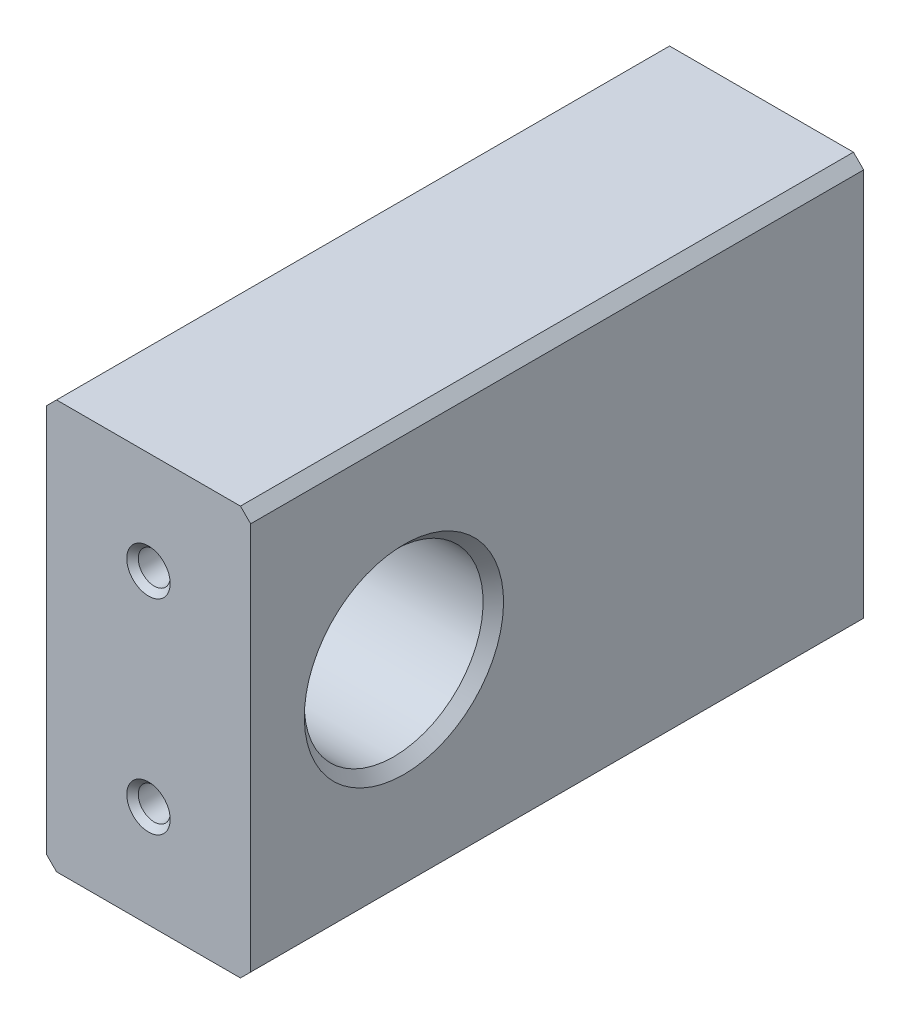
SolidWorks part; units mm, degrees
material "6061 Alloy"
ref_plane "Front" through (0, 0, 0) normal (0, 0, 1) x (1, 0, 0)
ref_plane "Top" through (0, 0, 0) normal (0, 1, 0) x (1, 0, 0)
ref_plane "Right" through (0, 0, 0) normal (1, 0, 0) x (0, 0, -1)
sketch "Sketch1" plane through (0, 0, 0) normal (0, 0, 1) x (1, 0, 0)
  line L0 (50.8, 0) -> (0, 0) construction
  line L1 (50.8, 50.8) -> (0, 50.8)
  line L2 (50.8, 50.8) -> (50.8, -50.8)
  line L3 (50.8, -50.8) -> (0, -50.8)
  line L4 (0, 50.8) -> (0, -50.8)
  dimension "D1" = 101.6
  dimension "D2" = 50.8
extrude "Extrude1" add sketch "Sketch1" along normal blind 152.4
sketch "Sketch2" plane through (50.8, 0, 0) normal (1, 0, 0) x (0, 0, -1)
  line L4 (-152.4, -50.8) -> (-152.4, 50.8) construction
  circle A0 centre (-114.3, 0) radius 22.225
  dimension "D1" = 44.45
  dimension "D2" = 38.1
extrude "Extrude2" cut sketch "Sketch2" against normal through all
chamfer "Chamfer1" distance 2.54 angle 45 5 edges at (0, 50.8, 76.2) (0, -50.8, 76.2) (50.8, -50.8, 76.2) (50.8, 22.225, 114.3) (50.8, 50.8, 76.2)
hole_wizard "3/8-16 Tapped Hole1" positions "Sketch4" profile "Sketch3" tap size "3/8-16" standard "Ansi Inch"
sketch "Sketch4" plane through (0, 0, 0) normal (0, 0, -1) x (-1, 0, 0)
  point P0 (-25.4, -25.4)
  point P1 (-25.4, 25.4)
  dimension "D1" = 50.8
  dimension "D2" = 25.4
  dimension "D3" = 25.4
cosmetic thread "Hole Thread1" parameters "D1"=19.05, "D2"=9.525
cosmetic thread "Hole Thread2" parameters "D1"=19.05, "D2"=9.525
sketch "Sketch3" plane through (25.4, -25.4, 0) normal (1, 0, 0) x (0, 1, 0)
  line L0 (0, 0) -> (0, 26.2607)
  line L1 (0, 26.2607) -> (3.9687, 23.876)
  line L2 (3.9687, 23.876) -> (3.9687, 1.4287)
  line L3 (3.9687, 1.4287) -> (5.3975, 0)
  line L5 (5.3975, 0) -> (0, 0)
  line L6 (-3.9687, 1.4287) -> (-5.3975, 0) construction
  line L10 (0, 26.2607) -> (-3.9688, 23.876) construction
  line L11 (0, -6.35) -> (0, 107.95) construction
  dimension "Tap Drill Dia." = 7.9375
  dimension "Tap Drill Depth" = 23.876
  dimension "Near C'Sink Dia." = 10.795
  dimension "Near C'Sink Angle" = 90
  dimension "Drill Angle" = 118
ref_plane "Plane1" through (0, 0, 76.2) normal (0, 0, -1) x (-1, 0, 0)
mirror "Mirror1" about plane through (0, 0, 76.2) normal (0, 0, -1) of "3/8-16 Tapped Hole1"
